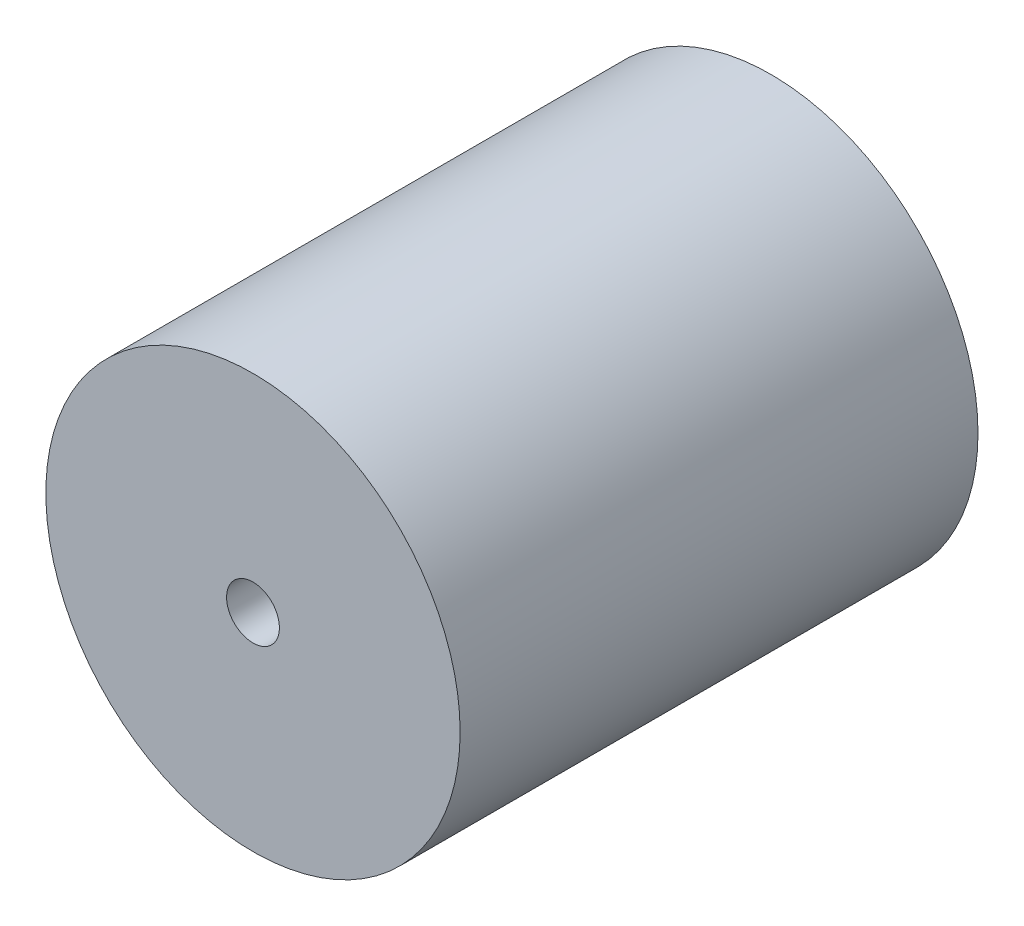
SolidWorks part; units mm, degrees
ref_plane "Ebene vorne" through (0, 0, 0) normal (0, 0, 1) x (1, 0, 0)
ref_plane "Ebene oben" through (0, 0, 0) normal (0, 1, 0) x (1, 0, 0)
ref_plane "Ebene rechts" through (0, 0, 0) normal (1, 0, 0) x (0, 0, -1)
sketch "Skizze1" plane through (0, 0, 0) normal (0, 0, 1) x (1, 0, 0)
  circle A0 centre (0, 0) radius 40
extrude "Aufsatz-Linear austragen1" add sketch "Skizze1" along normal blind 100
sketch "Skizze2" plane through (0, 0, 100) normal (0, 0, 1) x (1, 0, 0)
  circle A0 centre (0, 0) radius 5.1
extrude "Schnitt-Linear austragen1" cut sketch "Skizze2" against normal blind 25
cosmetic thread "Gewindedarstellung2" parameters "D1"=55, "D2"=12
equation "\"D__außen@Skizze1\"= 80"
equation "\"D1@Aufsatz-Linear austragen1\"= 100"
equation "\"Kernloch@Skizze2\"= 10.2"
equation "\"D1@Schnitt-Linear austragen1\"= 25"
